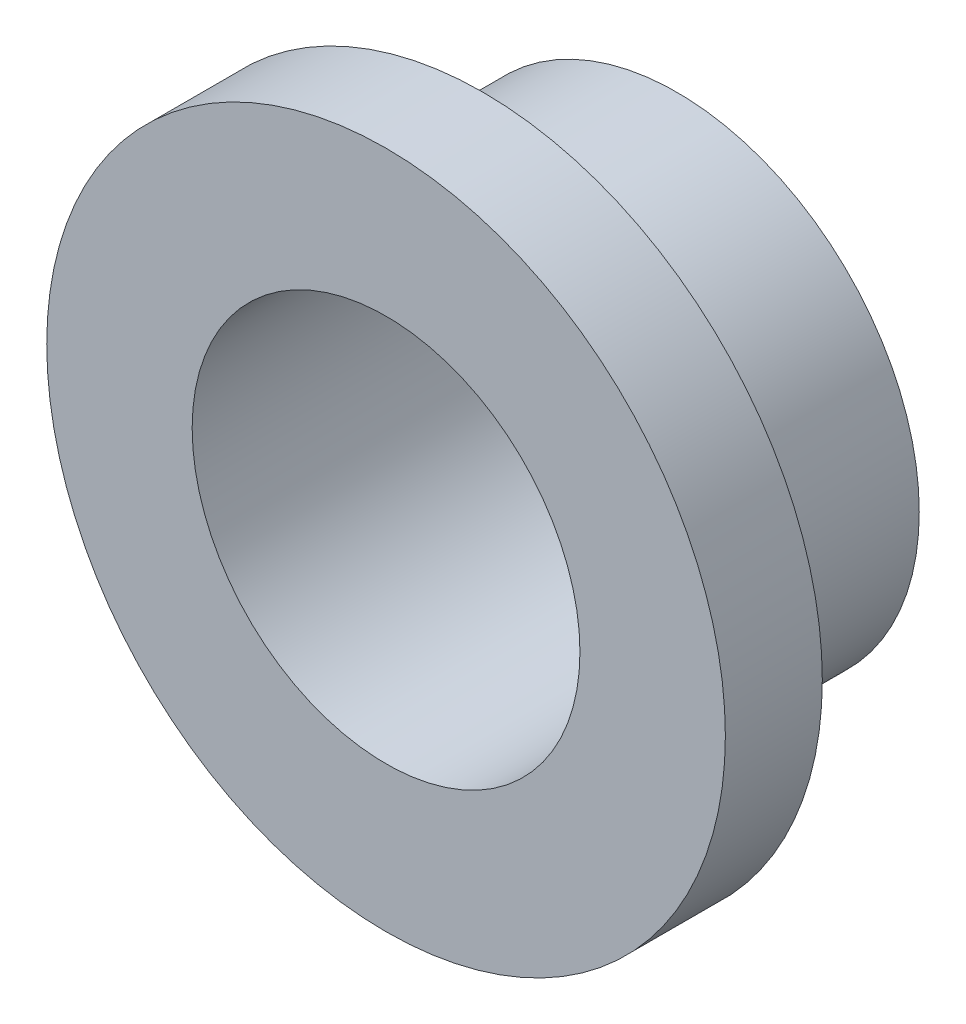
SolidWorks part; units mm, degrees
material "Aluminum Bronze"
ref_plane "Front Plane" through (0, 0, 0) normal (0, 0, 1) x (1, 0, 0)
ref_plane "Top Plane" through (0, 0, 0) normal (0, 1, 0) x (1, 0, 0)
ref_plane "Right Plane" through (0, 0, 0) normal (1, 0, 0) x (0, 0, -1)
sketch "Sketch1" plane through (0, 0, 0) normal (0, 0, 1) x (1, 0, 0)
  circle A0 centre (0, 0) radius 6.35
  circle A1 centre (0, 0) radius 7.9375
  dimension "D1" = 12.7
  dimension "D2" = 15.875
extrude "Boss-Extrude1" add sketch "Sketch1" along normal blind 9.525
sketch "Sketch2" plane through (0, 0, 9.525) normal (0, 0, 1) x (1, 0, 0)
  circle A0 centre (0, 0) radius 11.1125
  circle A1 centre (0, 0) radius 6.35 construction
  circle A2 centre (0, 0) radius 6.35
  dimension "D1" = 22.225
extrude "Boss-Extrude2" add sketch "Sketch2" against normal blind 3.175
